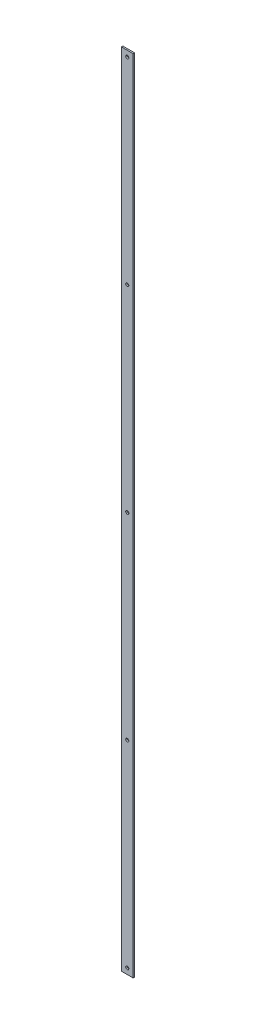
SolidWorks part; units mm, degrees
material "PC High Viscosity"
ref_plane "Front Plane" through (0, 0, 0) normal (0, 0, 1) x (1, 0, 0)
ref_plane "Top Plane" through (0, 0, 0) normal (0, 1, 0) x (1, 0, 0)
ref_plane "Right Plane" through (0, 0, 0) normal (1, 0, 0) x (0, 0, -1)
sketch "Sketch1" plane through (0, 0, 0) normal (0, 0, 1) x (1, 0, 0)
  line L0 (0, 0) -> (25.4, 0)
  line L1 (25.4, 0) -> (25.4, 1727.2)
  line L5 (0, 1727.2) -> (0, 0)
  line L6 (0, 1727.2) -> (25.4, 1727.2)
  dimension "D2" = 25.4
  dimension "D4" = 1727.2
extrude "Boss-Extrude1" add sketch "Sketch1" along normal blind 3.175
sketch "Sketch2" plane through (0, 0, 3.175) normal (0, 0, 1) x (1, 0, 0)
  line L0 (25.4, 0) -> (25.4, 1727.2) construction
  line L1 (0, 0) -> (25.4, 0) construction
  circle A0 centre (12.7, 12.7) radius 3.3655
  dimension "D1" = 6.731
  dimension "D2" = 12.7
  dimension "D3" = 12.7
extrude "Cut-Extrude1" cut sketch "Sketch2" against normal through all
pattern_linear "LPattern1" count 5 spacing 425.45 along (0, 1, 0) of "Cut-Extrude1"
